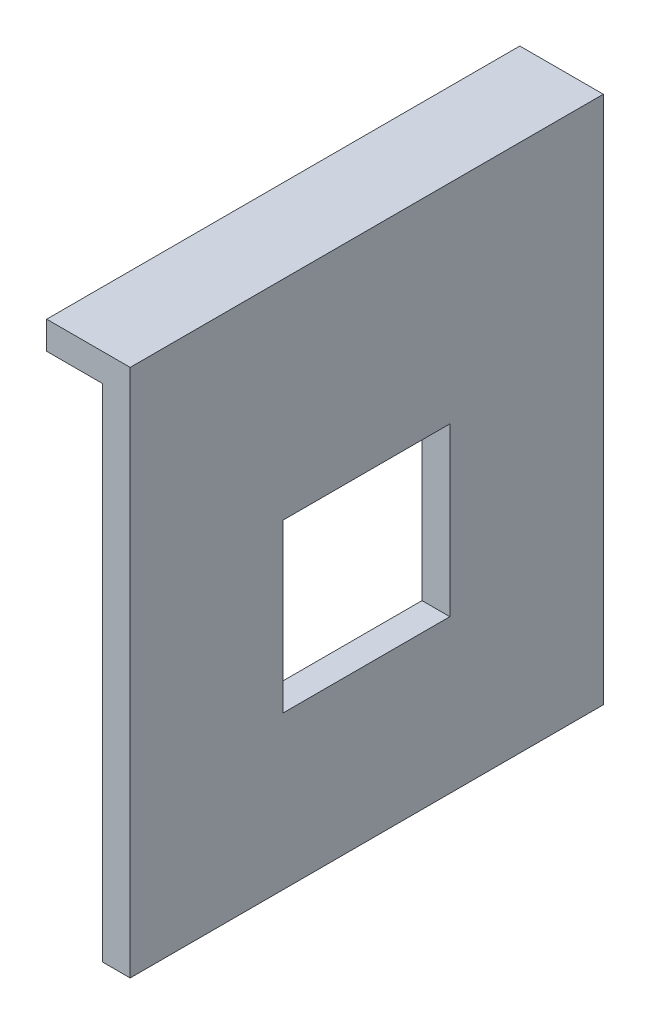
SolidWorks part; units mm, degrees
ref_plane "Front Plane" through (0, 0, 0) normal (0, 0, 1) x (1, 0, 0)
ref_plane "Top Plane" through (0, 0, 0) normal (0, 1, 0) x (1, 0, 0)
ref_plane "Right Plane" through (0, 0, 0) normal (1, 0, 0) x (0, 0, -1)
sketch "Sketch1" plane through (0, 0, 0) normal (0, 1, 0) x (1, 0, 0)
  line L1 (0, 0) -> (-5, 0)
  line L2 (0, 0) -> (0, -85)
  line L3 (0, -85) -> (-5, -85)
  line L4 (-5, 0) -> (-5, -85)
  dimension "D1" = 85
  dimension "D2" = 5
extrude "Boss-Extrude1" add sketch "Sketch1" along normal blind 95
sketch "Sketch2" plane through (-5, 0, 0) normal (-1, 0, 0) x (0, 0, 1)
  line L0 (85, 95) -> (85, 0) construction
  line L1 (0, 95) -> (85, 95)
  line L2 (0, 95) -> (0, 90)
  line L3 (0, 90) -> (85, 90)
  line L4 (85, 95) -> (85, 90)
  dimension "D1" = 5
extrude "Boss-Extrude2" add sketch "Sketch2" along normal blind 10
sketch "Sketch3" plane through (-5, 0, 0) normal (-1, 0, 0) x (0, 0, 1)
  line L0 (85, 90) -> (85, 0) construction
  line L1 (0, 0) -> (85, 0) construction
  line L3 (27.5736, 27.5) -> (57.5736, 27.5)
  line L4 (27.5736, 27.5) -> (27.5736, 57.5)
  line L5 (27.5736, 57.5) -> (57.5736, 57.5)
  line L6 (57.5736, 27.5) -> (57.5736, 57.5)
  line L7 (27.5736, 27.5) -> (57.5736, 57.5) construction
  line L8 (27.5736, 57.5) -> (57.5736, 27.5) construction
  circle A0 centre (42.5736, 42.5) radius 42.5
  point P4 (85, 45)
  point P5 (42.5736, 0)
  dimension "D2" = 85
  dimension "D1" = 42.5
  dimension "D3" = 0
  dimension "D4" = 30
  dimension "D5" = 30
extrude "Cut-Extrude1" cut sketch "Sketch3" against normal blind 10 contours L5 L6 L3 L4
